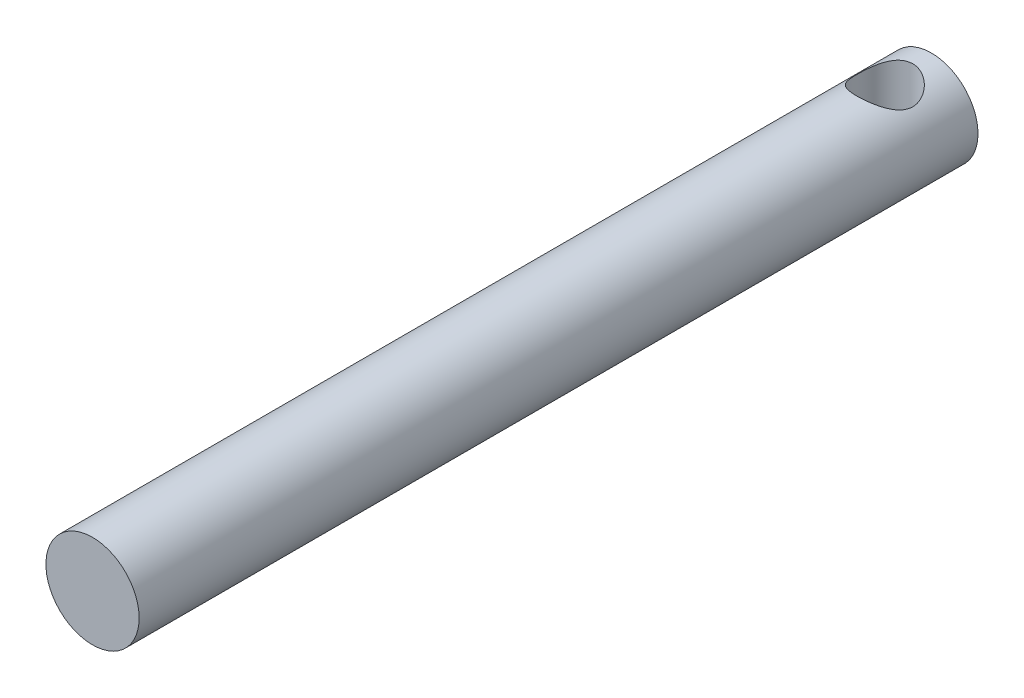
SolidWorks part; units mm, degrees
ref_plane "前视基准面" through (0, 0, 0) normal (0, 0, 1) x (1, 0, 0)
ref_plane "上视基准面" through (0, 0, 0) normal (0, 1, 0) x (1, 0, 0)
ref_plane "右视基准面" through (0, 0, 0) normal (1, 0, 0) x (0, 0, -1)
sketch "草图1" plane through (0, 0, 0) normal (0, 0, 1) x (1, 0, 0)
  circle A0 centre (-13.5092, 11.4107) radius 10
  dimension "D1" = 20
extrude "凸台-拉伸1" add sketch "草图1" along normal blind 180
sketch "草图2" plane through (0, 0, 0) normal (0, 1, 0) x (1, 0, 0)
  line L0 (-13.5092, -180) -> (-13.5092, -10) construction
  line L1 (-23.5092, -180) -> (-3.5092, -180) construction
  circle A0 centre (-13.5092, -10) radius 6
  dimension "D2" = 12
  dimension "D1" = 170
extrude "切除-拉伸2" cut sketch "草图2" along normal blind 97
